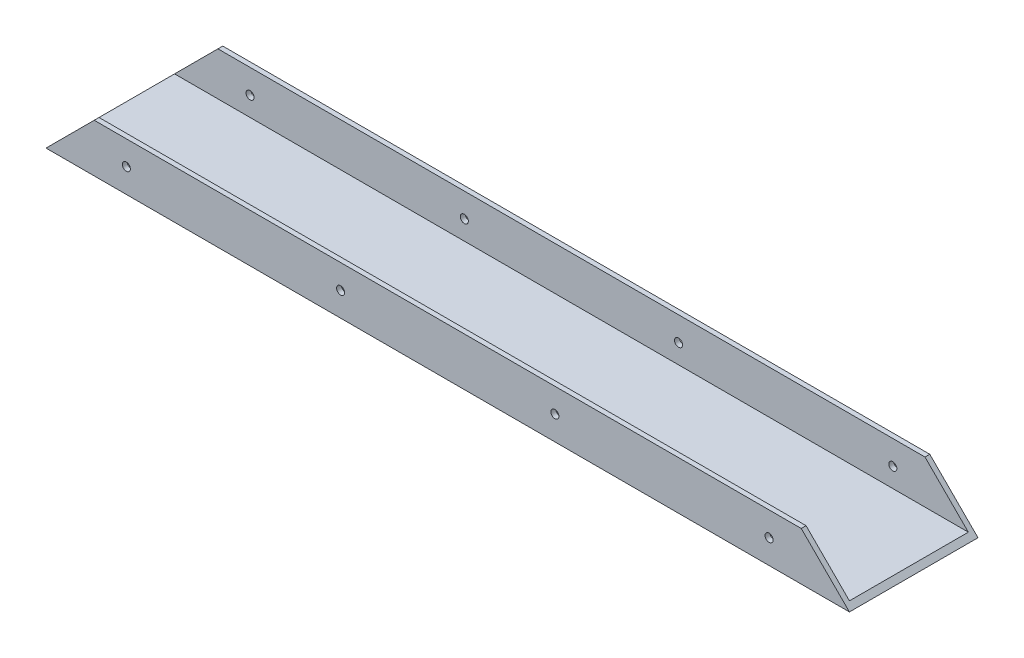
SolidWorks part; units mm, degrees
ref_plane "Alzado" through (0, 0, 0) normal (0, 0, 1) x (1, 0, 0)
ref_plane "Planta" through (0, 0, 0) normal (0, 1, 0) x (1, 0, 0)
ref_plane "Vista lateral" through (0, 0, 0) normal (1, 0, 0) x (0, 0, -1)
sketch "Croquis1" plane through (0, 0, 0) normal (1, 0, 0) x (0, 0, -1)
  line L0 (-20, 0) -> (20, 0)
  line L1 (20, 0) -> (20, 15)
  line L2 (20, 15) -> (18.5, 15)
  line L3 (18.5, 15) -> (18.5, 1.5)
  line L4 (18.5, 1.5) -> (-18.5, 1.5)
  line L5 (-18.5, 1.5) -> (-18.5, 15)
  line L6 (-18.5, 15) -> (-20, 15)
  line L7 (-20, 15) -> (-20, 0)
  point P4 (0, 0)
extrude "Saliente-Extruir1" add sketch "Croquis1" along normal blind 250
sketch "Croquis2" plane through (0, 0, -20) normal (0, 0, -1) x (-1, 0, 0)
  line L3 (0, 15) -> (-15, 15)
  line L4 (-250, 15) -> (0, 15) construction
  line L5 (-15, 15) -> (0, 0)
  line L6 (0, 0) -> (0, 15)
  line L7 (-250, 15) -> (-235, 15)
  line L8 (-235, 15) -> (-250, 0)
  line L9 (-250, 0) -> (0, 0) construction
  line L10 (-250, 0) -> (-250, 15) construction
  line L11 (-250, 0) -> (-250, 15)
  line L12 (-125, 0) -> (-125, 15) construction
  line L13 (-125, 0) -> (-125, 7.5) construction
  line L14 (-25, 7.5) -> (-91.6667, 7.5) construction
  line L15 (-91.6667, 7.5) -> (-158.3333, 7.5) construction
  line L16 (-242.5, 7.5) -> (-225, 7.5) construction
  line L17 (-158.3333, 7.5) -> (-225, 7.5) construction
  line L18 (-225, 7.5) -> (-242.5, 7.5) construction
  line L21 (-250, 15) -> (0, 15) construction
  circle A7 centre (-225, 7.5) radius 1.25
  circle A8 centre (-25, 7.5) radius 1.25
  circle A9 centre (-158.3333, 7.5) radius 1.25
  circle A10 centre (-91.6667, 7.5) radius 1.25
  point P29 (-125, 0)
extrude "Cortar-Extruir1" cut sketch "Croquis2" against normal through all
